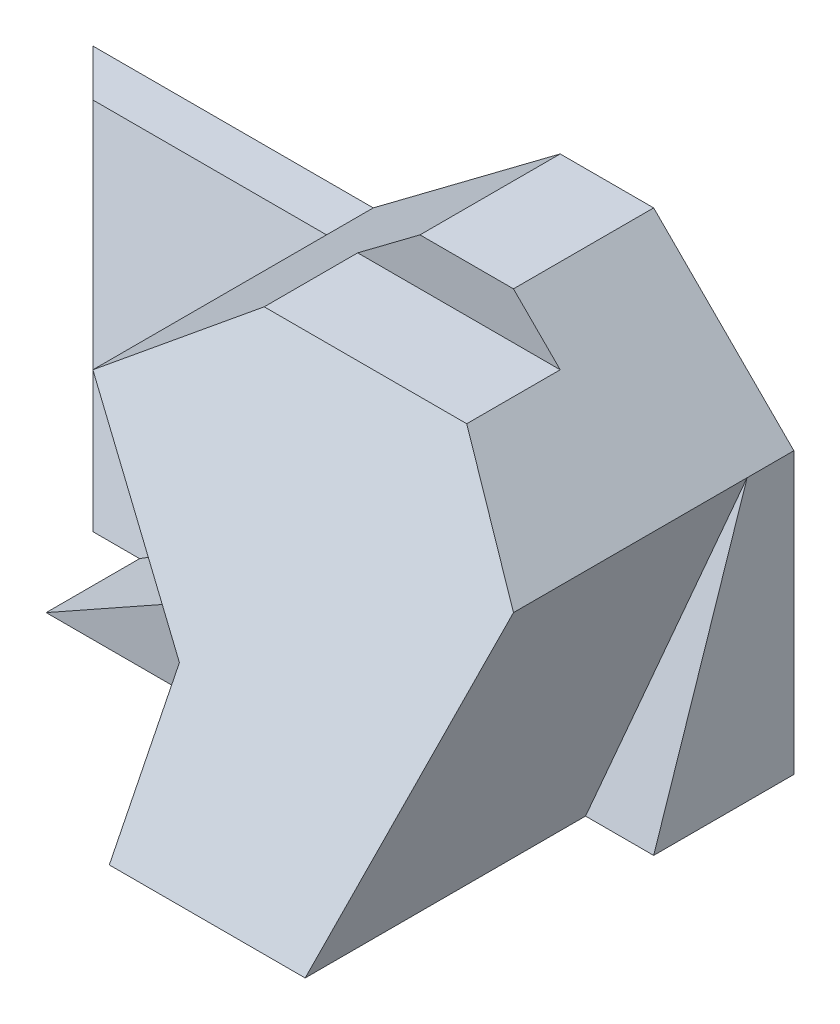
SolidWorks part; units mm, degrees
ref_plane "Front" through (0, 0, 0) normal (0, 0, 1) x (1, 0, 0)
ref_plane "Top" through (0, 0, 0) normal (0, 1, 0) x (1, 0, 0)
ref_plane "Right" through (0, 0, 0) normal (1, 0, 0) x (0, 0, -1)
sketch "Sketch1" plane through (0, 0, 0) normal (0, 0, 1) x (1, 0, 0)
  line L0 (4.5, 4.5) -> (7.5, 1.5)
  line L1 (-7.5, -4.5) -> (7.5, -4.5)
  line L2 (-7.5, -4.5) -> (-7.5, 4.5)
  line L3 (-7.5, 4.5) -> (7.5, 4.5)
  line L4 (7.5, -4.5) -> (7.5, 4.5)
  line L5 (-7.5, -4.5) -> (7.5, 4.5) construction
  line L6 (-7.5, 4.5) -> (7.5, -4.5) construction
  line L7 (2.5, 4.5) -> (-1.5, 1.5)
  line L8 (-1.5, 1.5) -> (-7.5, 1.5)
  point P0 (0, 0)
  dimension "D1" = 9
  dimension "D2" = 15
  dimension "D3" = 3
  dimension "D4" = 3
  dimension "D5" = 3
  dimension "D6" = 4
  dimension "D7" = 6
extrude "Boss-Extrude1" add sketch "Sketch1" along normal blind 9 contours L7 L8 L2 L1 L4 L0 L3
sketch "Sketch2" plane through (-7.5, 0, 0) normal (-1, 0, 0) x (0, 0, 1)
  line L0 (3, 4.5) -> (3, 3.5)
  line L1 (9, 4.5) -> (0, 4.5) construction
  line L2 (3, 3.5) -> (5, 3.5)
  line L3 (5, 3.5) -> (9, -4.5)
  line L4 (9, -4.5) -> (9, 4.5)
  line L5 (9, 4.5) -> (3, 4.5)
  dimension "D1" = 1
  dimension "D2" = 2
  dimension "D3" = 6
extrude "Cut-Extrude1" cut sketch "Sketch2" against normal blind 19
sketch3d "3DSketch1"
  line L0 (-7.5, 1.5, 0) -> (-7.5, -4.5, 0)
  line L1 (-7.5, -4.5, 0) -> (-4.5, -4.5, 3)
  line L2 (-4.5, -4.5, 3) -> (-6.5, 1.5, 1)
  line L3 (-6.5, 1.5, 1) -> (-7.5, 1.5, 0)
  point P6 (0, 0, 0)
  point P7 (0, 0, 0)
  point P8 (0, 0, 0)
  point P9 (0, 0, 0)
  point P10 (0, 0, 0)
  point P11 (0, 0, 0)
  point P12 (0, 0, 0)
  dimension "D1" = 1
  dimension "D2" = 1
  dimension "D3" = 3
  dimension "D4" = 1
  dimension "D5" = 3
extrude "Cut-Extrude2" cut sketch "3DSketch1" along direction (-1, 0, 0) on the side against the normal blind 10
sketch3d "3DSketch2"
  line L0 (-6.5, 1.5, 1) -> (-4.5, -4.5, 3)
  line L1 (-4.5, -4.5, 3) -> (-3.5, -4.5, 3)
  line L2 (-3.5, -4.5, 3) -> (1.8518, -1.5, 2)
  line L3 (1.8518, -1.5, 2) -> (-1.5, 1.5, 1)
  line L4 (-1.5, 1.5, 1) -> (-6.5, 1.5, 1)
  line L5 (-1.5, 1.5, 6) -> (-1.5, 1.5, 0) construction
  point P7 (0.9425, 1.4067, -0.8174)
  point P8 (2.6147, -3.9822, 1.4613)
  point P9 (-1.5, 1.5, 1.1411)
  dimension "D1" = 1
  dimension "D2" = 3
  dimension "D3" = 2
  dimension "D4" = 1
extrude "Cut-Extrude3" cut sketch "3DSketch2" along direction (0, 0, 1) on the side against the normal blind 10
sketch3d "3DSketch3"
  line L0 (7.5, 1.5, 1) -> (7.5, -4.5, 3)
  line L1 (7.5, -4.5, 9) -> (7.5, -4.5, 0) construction
  line L2 (7.5, -4.5, 3) -> (6.0427, -4.5, 3)
  line L3 (6.0427, -4.5, 3) -> (7.5, 1.5, 1)
  point P6 (0, 0, 0)
  dimension "D1" = 3
extrude "Cut-Extrude4" cut sketch "3DSketch3" along direction (0, 0, 1) on the side of the normal blind 10
ref_plane "Plane1" through (0, 0, 10) normal (0, 0, 1) x (1, 0, 0)
sketch "Sketch4" plane through (0, 0, 10) normal (0, 0, 1) x (1, 0, 0)
  line L0 (1.8518, -1.5) -> (1.8518, -4.5)
  line L7 (6.0427, -4.5) -> (7.5, 1.5)
  line L8 (7.5, 1.5) -> (5.5, 3.5)
  line L9 (5.5, 3.5) -> (1.1667, 3.5)
  line L10 (1.1667, 3.5) -> (-1.5, 1.5)
  line L11 (-1.5, 1.5) -> (1.8518, -1.5)
  line L12 (1.8518, -1.5) -> (-3.5, -4.5)
  line L13 (-3.5, -4.5) -> (6.0427, -4.5)
  line L14 (6.0427, -4.5) -> (7.5, 1.5)
  line L15 (7.5, 1.5) -> (5.5, 3.5)
  line L16 (5.5, 3.5) -> (1.1667, 3.5)
  line L17 (1.1667, 3.5) -> (-1.5, 1.5)
  line L18 (-1.5, 1.5) -> (1.8518, -1.5)
  line L19 (1.8518, -1.5) -> (-3.5, -4.5)
  line L20 (-3.5, -4.5) -> (6.0427, -4.5)
  dimension "D1" = 0
extrude "Cut-Extrude6" cut sketch "Sketch4" against normal blind 5 contours L19 L20 L0
